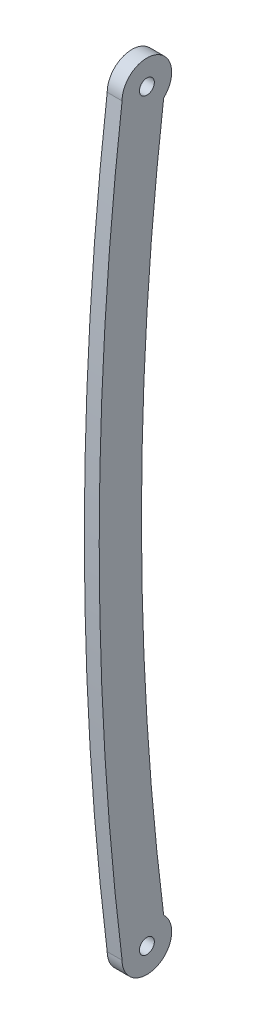
SolidWorks part; units mm, degrees
ref_plane "Alzado" through (0, 0, 0) normal (0, 0, 1) x (1, 0, 0)
ref_plane "Planta" through (0, 0, 0) normal (0, 1, 0) x (1, 0, 0)
ref_plane "Vista lateral" through (0, 0, 0) normal (1, 0, 0) x (0, 0, -1)
sketch "Croquis1" plane through (0, 0, 0) normal (1, 0, 0) x (0, 0, -1)
  line L0 (0, 0) -> (0, 150) construction
  arc A0 (-5, 0) -> (3.3815, 3.6831) centre (0, 0) ccw
  arc A1 (3.3815, 146.3169) -> (-5, 150) centre (0, 150) ccw
  arc A2 (-5, 0) -> (-5, 150) centre (603.1154, 75) cw
  arc A3 (3.3815, 146.3169) -> (3.3815, 3.6831) centre (569.0801, 75) ccw
  circle A4 centre (0, 150) radius 1.5
  circle A5 centre (0, 0) radius 1.5
  dimension "D1" = 3
  dimension "D2" = 612.7229
  dimension "D3" = 570.1763
  dimension "D4" = 3.3815
extrude "Saliente-Extruir1" add sketch "Croquis1" along normal blind 3
